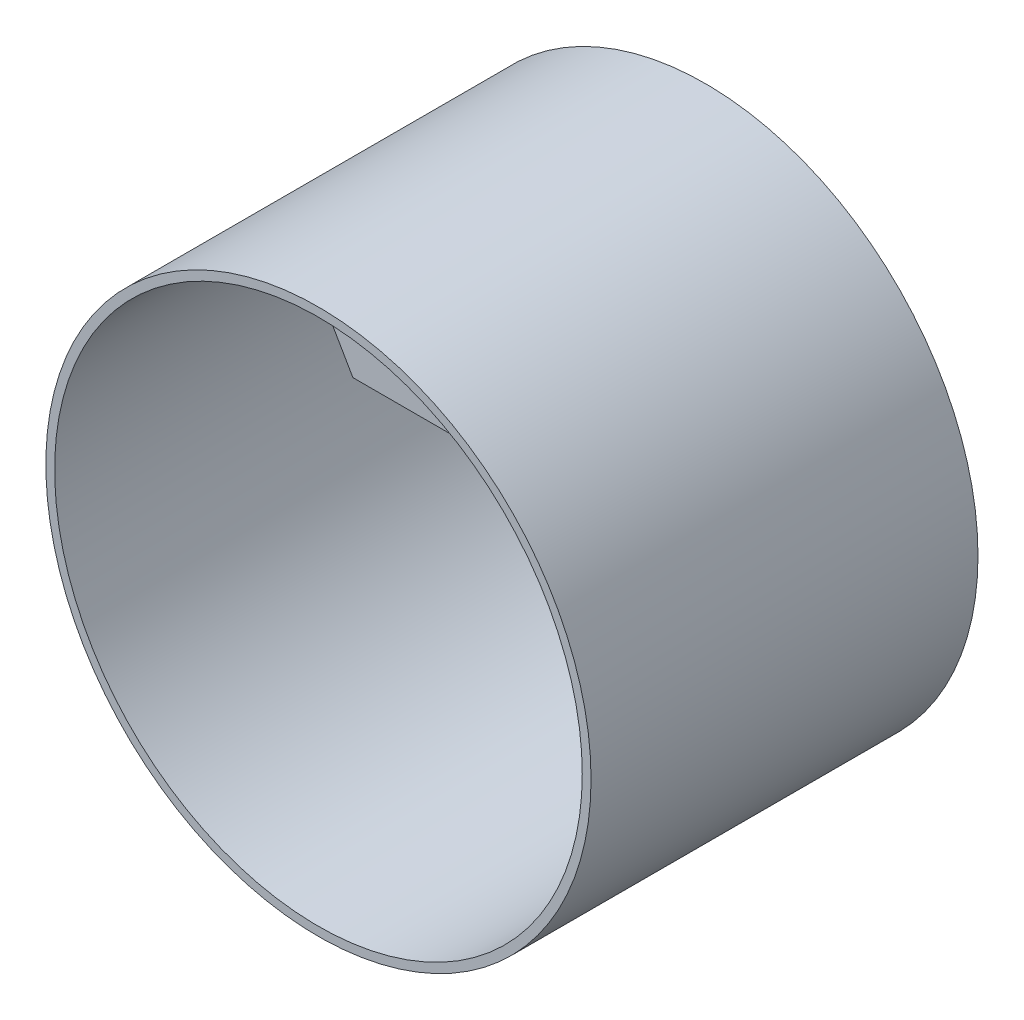
SolidWorks part; units mm, degrees
ref_plane "前视基准面" through (0, 0, 0) normal (0, 0, 1) x (1, 0, 0)
ref_plane "上视基准面" through (0, 0, 0) normal (0, 1, 0) x (1, 0, 0)
ref_plane "右视基准面" through (0, 0, 0) normal (1, 0, 0) x (0, 0, -1)
other "Configuration Table"
sketch "草图1" plane through (0, 0, 0) normal (0, 0, 1) x (1, 0, 0)
  circle A0 centre (0, 0) radius 150
  circle A1 centre (0, 0) radius 155
extrude "凸台-拉伸1" add sketch "草图1" along normal mid plane 220
sketch "草图2" plane through (0, 0, 0) normal (0, 0, 1) x (1, 0, 0)
  line L0 (0, 0) -> (0, 150) construction
  line L1 (-40.4145, 70) -> (-75, 129.9038)
  line L2 (40.4145, 70) -> (75, 129.9038)
  line L3 (-40.4145, 70) -> (40.4145, 70)
  circle A1 centre (0, 0) radius 150 construction
  arc A2 (75, 129.9038) -> (-75, 129.9038) centre (0, 0) ccw
  dimension "D1" = 30
  dimension "D2" = 70
extrude "凸台-拉伸2" add sketch "草图2" along normal mid plane 100
